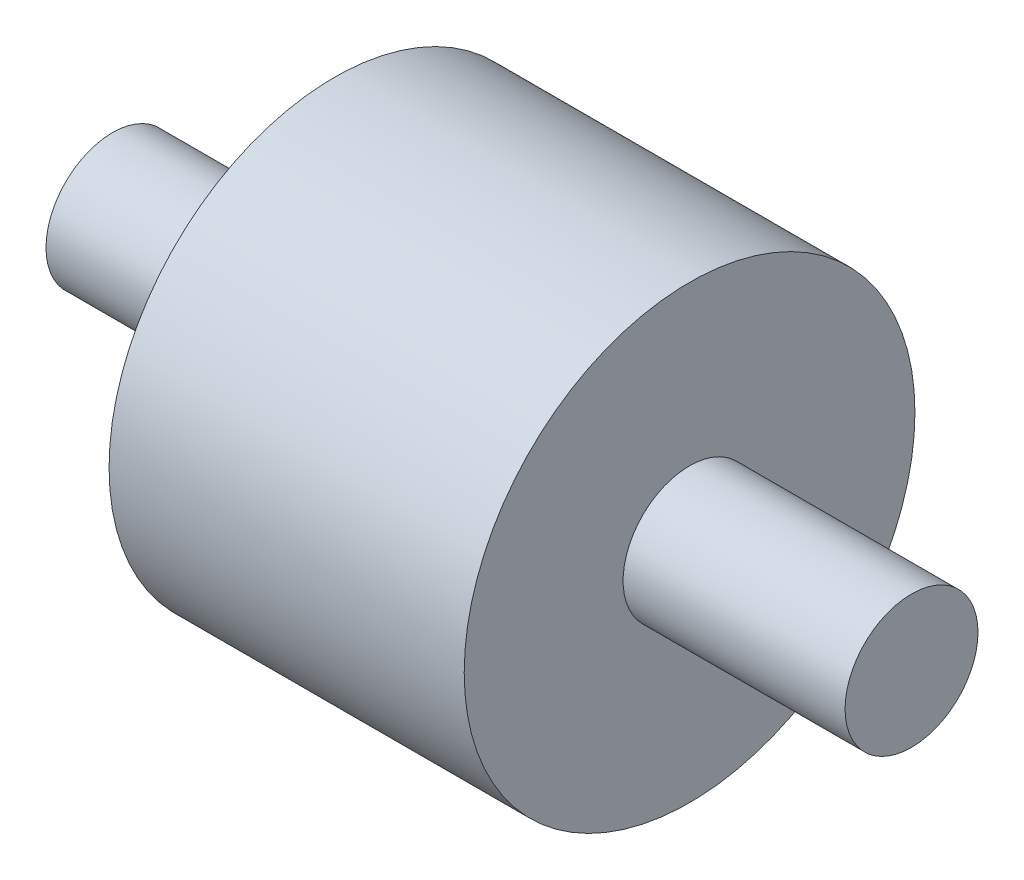
SolidWorks part; units mm, degrees
ref_plane "Front Plane" through (0, 0, 0) normal (0, 0, 1) x (1, 0, 0)
ref_plane "Top Plane" through (0, 0, 0) normal (0, 1, 0) x (1, 0, 0)
ref_plane "Right Plane" through (0, 0, 0) normal (1, 0, 0) x (0, 0, -1)
sketch "Sketch1" plane through (0, 0, 0) normal (1, 0, 0) x (0, 0, -1)
  circle A0 centre (0, 0) radius 25.3837
  circle A1 centre (0, 0) radius 7.5564
  dimension "D1" = 50.7674
  dimension "D2" = 15.1127
extrude "Boss-Extrude1" add sketch "Sketch1" along normal blind 40 contours A0
sketch "Sketch2" plane through (0, 0, 0) normal (-1, 0, 0) x (0, 0, 1)
  circle A0 centre (0, 0) radius 7.4859
  dimension "D1" = 14.9718
extrude "Boss-Extrude2" add sketch "Sketch2" against normal blind 65 and the other way blind 25 contours A0
